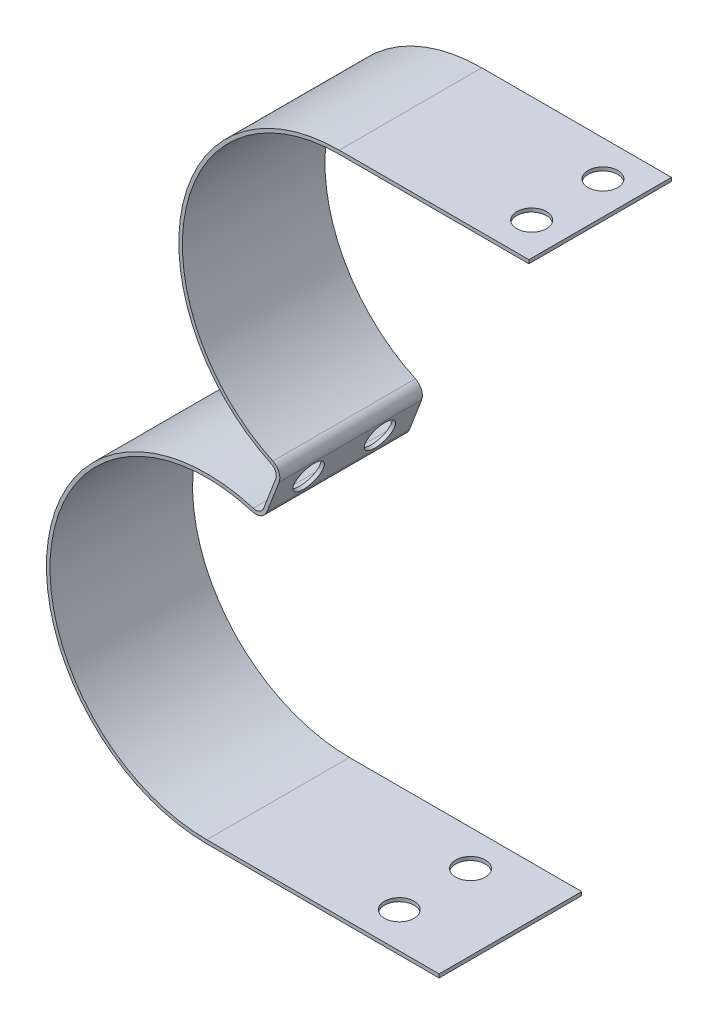
SolidWorks part; units mm, degrees
material "Plain Carbon Steel"
ref_plane "Front Plane" through (0, 0, 0) normal (0, 0, 1) x (1, 0, 0)
ref_plane "Top Plane" through (0, 0, 0) normal (0, 1, 0) x (1, 0, 0)
ref_plane "Right Plane" through (0, 0, 0) normal (1, 0, 0) x (0, 0, -1)
sketch "Sketch1" plane through (0, 0, 0) normal (0, 0, 1) x (1, 0, 0)
  line L0 (12.4739, 32.6214) -> (-41.9576, -109.7267) construction
  line L1 (-17.0098, -44.4838) -> (-12.4739, -32.6214)
  line L2 (-29.4837, -112.0302) -> (22.258, -112.0302)
  line L3 (0, 34.925) -> (42.2499, 34.925)
  line L4 (0, 35.7188) -> (42.2499, 35.7188)
  line L5 (-17.4709, -43.4671) -> (-13.4956, -33.0711)
  line L6 (-29.4837, -112.824) -> (22.258, -112.824)
  line L7 (22.258, -112.0302) -> (22.258, -112.824)
  line L8 (42.2499, 35.7188) -> (42.2499, 34.925)
  line L9 (0, 0) -> (46.7341, 0) construction
  arc A0 (0, 34.925) -> (-12.4739, -32.6214) centre (0, 0) ccw
  arc A1 (-17.0098, -44.4838) -> (-29.4837, -112.0302) centre (-29.4837, -77.1052) ccw
  arc A2 (0, 35.7188) -> (-13.4956, -33.0711) centre (0, 0) ccw
  arc A3 (-17.4709, -43.4671) -> (-29.4837, -112.824) centre (-29.4837, -77.1052) ccw
  dimension "D1" = 69.85
  dimension "D2" = 69.85
  dimension "D3" = 82.55
  dimension "D5" = 110.926
  dimension "D4" = 0.7937
extrude "Boss-Extrude1" add sketch "Sketch1" along normal blind 31.75
sketch "Sketch2" plane through (-0.7414, 0.2835, 0) normal (-0.934, 0.3572, 0) x (0, 0, 1)
  line L0 (0, -41.275) -> (31.75, -41.275) construction
  line L1 (0, -35.7099) -> (0, -46.8401) construction
  line L2 (31.75, -35.7099) -> (31.75, -46.8401) construction
  circle A0 centre (7.9375, -41.275) radius 3.302
  circle A1 centre (23.8125, -41.275) radius 3.302
  dimension "D1" = 6.604
  dimension "D2" = 6.604
  dimension "D3" = 15.875
  dimension "D4" = 7.9375
extrude "Cut-Extrude1" cut sketch "Sketch2" against normal through all
sketch "Sketch3" plane through (0, 35.7188, 0) normal (0, 1, 0) x (1, 0, 0)
  line L0 (34.925, 0) -> (34.925, -31.75) construction
  line L1 (42.2499, 0) -> (0, 0) construction
  line L2 (42.2499, -31.75) -> (0, -31.75) construction
  line L3 (0, -31.75) -> (0, 0) construction
  circle A0 centre (34.925, -7.9375) radius 3.302
  circle A1 centre (34.925, -23.8125) radius 3.302
  dimension "D1" = 6.604
  dimension "D2" = 6.604
  dimension "D3" = 15.875
  dimension "D4" = 7.9375
  dimension "D5" = 34.925
extrude "Cut-Extrude2" cut sketch "Sketch3" against normal blind 31.75
sketch "Sketch4" plane through (0, -112.824, 0) normal (0, -1, 0) x (1, 0, 0)
  line L0 (5.4413, 31.75) -> (5.4413, 0) construction
  line L1 (-29.4837, 31.75) -> (22.258, 31.75) construction
  line L2 (-29.4837, 0) -> (22.258, 0) construction
  line L3 (-29.4837, 31.75) -> (-29.4837, 0) construction
  circle A0 centre (5.4413, 23.8125) radius 3.302
  circle A1 centre (5.4413, 7.9375) radius 3.302
  dimension "D1" = 6.604
  dimension "D2" = 6.604
  dimension "D3" = 15.875
  dimension "D4" = 7.9375
  dimension "D5" = 34.925
extrude "Cut-Extrude3" cut sketch "Sketch4" against normal blind 31.75
fillet "Fillet1" radius 1.905 2 edges at (-17.4709, -43.4671, 15.875) (-13.4956, -33.0711, 15.875)
fillet "Fillet2" radius 2.6987 2 edges at (-12.4739, -32.6214, 15.875) (-17.0098, -44.4838, 15.875)
